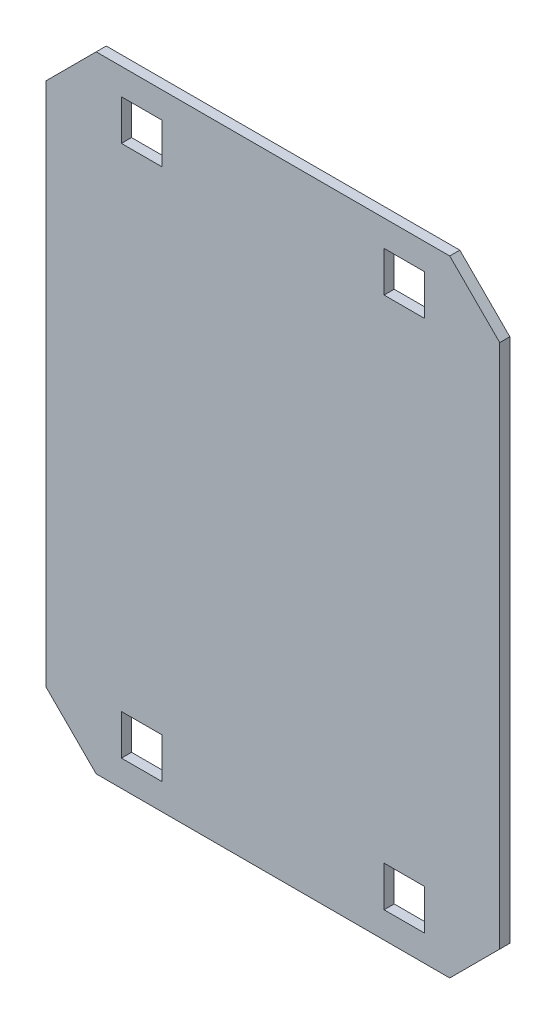
SolidWorks part; units mm, degrees
ref_plane "Plan de face" through (0, 0, 0) normal (0, 0, 1) x (1, 0, 0)
ref_plane "Plan de dessus" through (0, 0, 0) normal (0, 1, 0) x (1, 0, 0)
ref_plane "Plan de droite" through (0, 0, 0) normal (1, 0, 0) x (0, 0, -1)
sketch "Esquisse1" plane through (0, 0, 0) normal (0, 0, 1) x (1, 0, 0)
  line L0 (-112.2487, -130) -> (-87.5, -154.7487)
  line L7 (0, 154.7487) -> (0, -154.7487) construction
  line L8 (-112.2487, 0) -> (112.2487, 0) construction
  line L9 (-112.2487, 130) -> (-87.5, 154.7487)
  line L10 (112.2487, 130) -> (87.5, 154.7487)
  line L11 (112.2487, -130) -> (87.5, -154.7487)
  line L12 (-112.2487, 130) -> (-112.2487, -130)
  line L13 (-87.5, 154.7487) -> (87.5, 154.7487)
  line L14 (112.2487, 130) -> (112.2487, -130)
  line L15 (87.5, -154.7487) -> (-87.5, -154.7487)
  point P0 (0, 0)
  dimension "D1" = 260
  dimension "D2" = 175
  dimension "D3" = 35
  dimension "D4" = 135
extrude "Boss.-Extru.1" add sketch "Esquisse1" along normal blind 5
sketch "Esquisse2" plane through (0, 0, 5) normal (0, 0, 1) x (1, 0, 0)
  line L1 (-75, 141.7487) -> (-55, 141.7487)
  line L2 (-75, 141.7487) -> (-75, 121.7487)
  line L3 (-75, 121.7487) -> (-55, 121.7487)
  line L4 (-55, 141.7487) -> (-55, 121.7487)
  line L5 (-75, 141.7487) -> (-55, 121.7487) construction
  line L6 (-75, 121.7487) -> (-55, 141.7487) construction
  line L9 (0, 154.7487) -> (0, -154.7487) construction
  line L10 (-87.5, 154.7487) -> (87.5, 154.7487) construction
  line L11 (0, 154.7487) -> (0, -154.7487) construction
  line L12 (-112.2487, 0) -> (112.2487, 0) construction
  line L13 (-75, -121.7487) -> (-55, -141.7487) construction
  line L14 (-75, -141.7487) -> (-55, -121.7487) construction
  line L15 (-55, -141.7487) -> (-55, -121.7487)
  line L16 (-75, -121.7487) -> (-55, -121.7487)
  line L17 (-75, -141.7487) -> (-75, -121.7487)
  line L18 (-75, -141.7487) -> (-55, -141.7487)
  line L19 (75, -141.7487) -> (55, -121.7487) construction
  line L20 (75, -121.7487) -> (55, -141.7487) construction
  line L21 (75, -141.7487) -> (55, -141.7487)
  line L22 (75, -141.7487) -> (75, -121.7487)
  line L23 (75, -121.7487) -> (55, -121.7487)
  line L24 (55, -141.7487) -> (55, -121.7487)
  line L25 (75, 121.7487) -> (55, 141.7487) construction
  line L26 (75, 141.7487) -> (55, 121.7487) construction
  line L27 (55, 141.7487) -> (55, 121.7487)
  line L28 (75, 121.7487) -> (55, 121.7487)
  line L29 (75, 141.7487) -> (75, 121.7487)
  line L30 (75, 141.7487) -> (55, 141.7487)
  point P0 (-65, 131.7487)
  point P21 (-65, -131.7487)
  point P26 (65, -131.7487)
  point P31 (65, 131.7487)
  dimension "D1" = 65
  dimension "D2" = 23
  dimension "D3" = 20
  dimension "D4" = 20
extrude "Enlèv. mat.-Extru.1" cut sketch "Esquisse2" against normal blind 5
